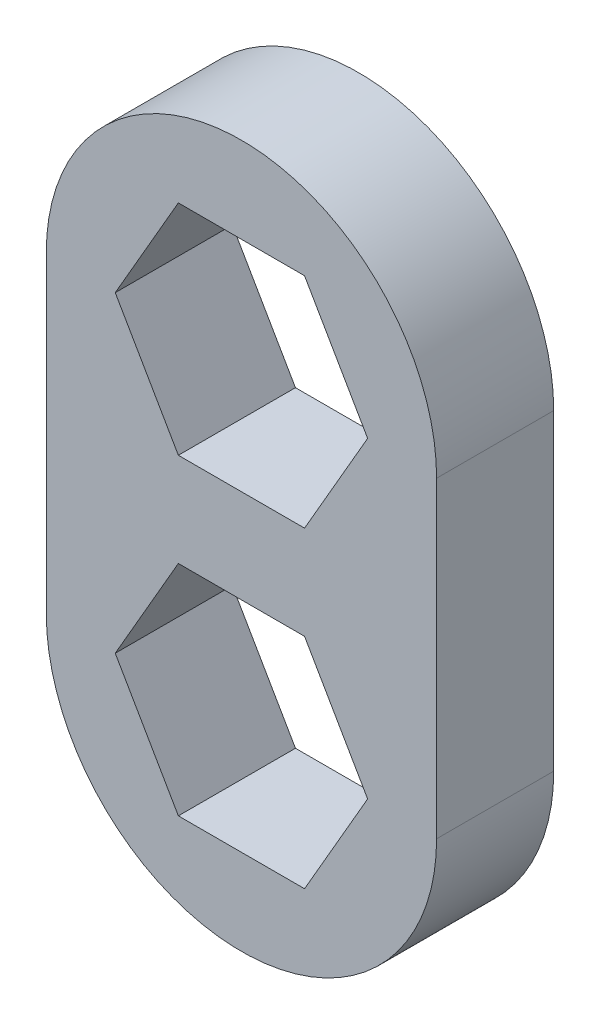
SolidWorks part; units mm, degrees
ref_plane "Front Plane" through (0, 0, 0) normal (0, 0, 1) x (1, 0, 0)
ref_plane "Top Plane" through (0, 0, 0) normal (0, 1, 0) x (1, 0, 0)
ref_plane "Right Plane" through (0, 0, 0) normal (1, 0, 0) x (0, 0, -1)
sketch "Sketch1" plane through (0, 0, 0) normal (0, 0, 1) x (1, 0, 0)
  line L0 (0, 4) -> (0, -4) construction
  line L1 (1.6166, 1.2) -> (3.2332, 4)
  line L2 (3.2332, 4) -> (1.6166, 6.8)
  line L3 (1.6166, 6.8) -> (-1.6166, 6.8)
  line L4 (-1.6166, 6.8) -> (-3.2332, 4)
  line L5 (-3.2332, 4) -> (-1.6166, 1.2)
  line L6 (-1.6166, 1.2) -> (1.6166, 1.2)
  line L7 (3.2332, -4) -> (1.6166, -1.2)
  line L8 (1.6166, -1.2) -> (-1.6166, -1.2)
  line L9 (-1.6166, -1.2) -> (-3.2332, -4)
  line L10 (-3.2332, -4) -> (-1.6166, -6.8)
  line L11 (-1.6166, -6.8) -> (1.6166, -6.8)
  line L12 (1.6166, -6.8) -> (3.2332, -4)
  line L13 (-5, -4) -> (-5, 4)
  line L14 (5, 4) -> (5, -4)
  circle A0 centre (0, 4) radius 2.8 construction
  circle A1 centre (0, -4) radius 2.8 construction
  arc A2 (-5, 4) -> (5, 4) centre (0, 4) cw
  arc A3 (5, -4) -> (-5, -4) centre (0, -4) cw
  point P18 (0, -4.137)
  point P21 (0, 0)
  point P23 (0.1324, 4)
  point P24 (0, 0)
  point P25 (0, 0)
  dimension "D3" = 5
  dimension "D1" = 5.6
  dimension "D2" = 8
extrude "Boss-Extrude1" add sketch "Sketch1" along normal blind 3
